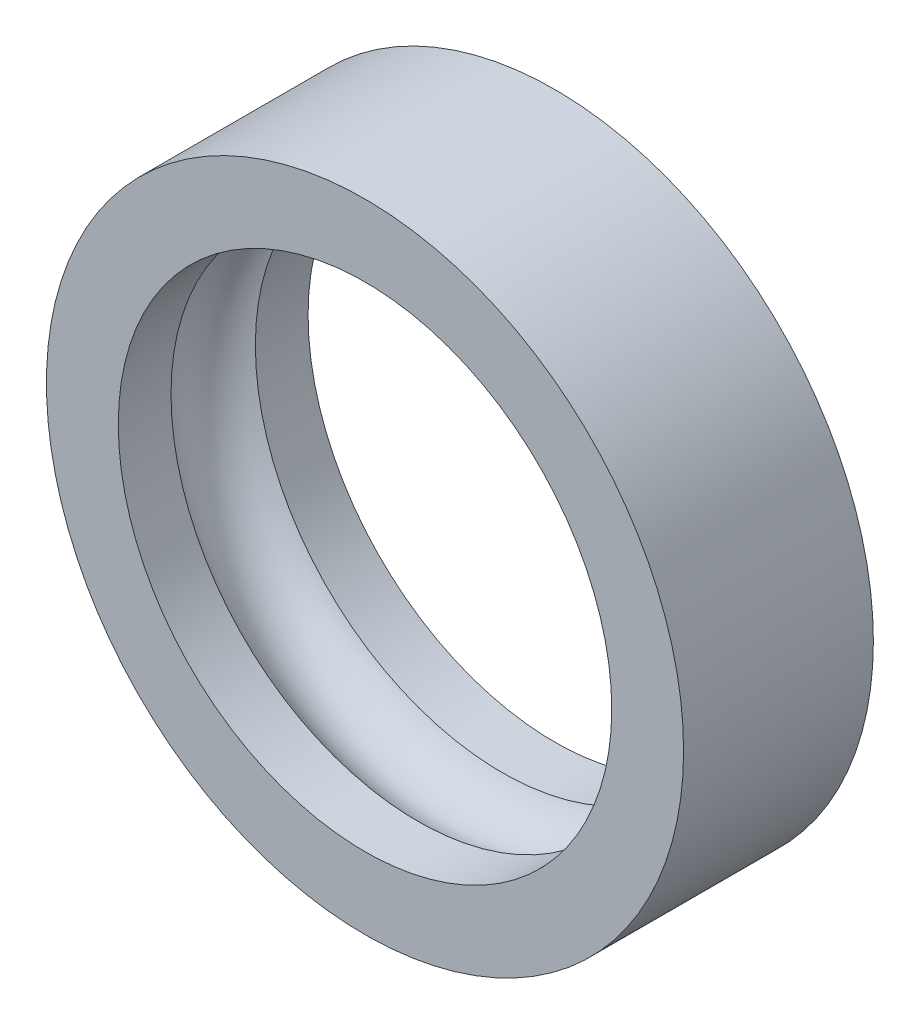
SolidWorks part; units mm, degrees
ref_plane "Front Plane" through (0, 0, 0) normal (0, 0, 1) x (1, 0, 0)
ref_plane "Top Plane" through (0, 0, 0) normal (0, 1, 0) x (1, 0, 0)
ref_plane "Right Plane" through (0, 0, 0) normal (1, 0, 0) x (0, 0, -1)
sketch "Sketch1" plane through (0, 0, 0) normal (1, 0, 0) x (0, 0, -1)
  line L0 (-7, 0) -> (7, 0) construction
  line L1 (0, 23.5) -> (0, -23.5) construction
  line L2 (6.3, 23.5) -> (-6.3, 23.5)
  line L4 (-7, 22.8) -> (-7, 18.2005)
  line L5 (-7, 18.2005) -> (-3.1111, 18.2005)
  line L6 (7, 18.2005) -> (3.1111, 18.2005)
  line L7 (7, 22.8) -> (7, 18.2005)
  line L9 (0, 23.5) -> (0, 16.75) construction
  line L10 (0, 16.75) -> (0, 10) construction
  line L11 (-7, 22.8) -> (-7, 23.5)
  line L12 (-7, 23.5) -> (-6.3, 23.5)
  line L13 (7, 22.8) -> (7, 23.5)
  line L14 (7, 23.5) -> (6.3, 23.5)
  arc A0 (-3.1111, 18.2005) -> (3.1111, 18.2005) centre (0, 16.75) cw
  point P14 (0, 10)
  dimension "Width" = 14
  dimension "OD" = 47
  dimension "D2" = 0.7
  dimension "Shaft Dia" = 20
  dimension "D3" = 6.2222
  dimension "D4" = 1.4505
revolve "Revolve1" add sketch "Sketch1" angle 360 about L0
equation "\"D2@Sketch1\" = \"Width@Sketch1\"*.05"
equation "\"D3@Sketch1\" = \"Width@Sketch1\"/2.25"
equation "\"D4@Sketch1\" = (((\"OD@Sketch1\"-\"Width@Sketch1\")/2)/3.25)/3.5"
